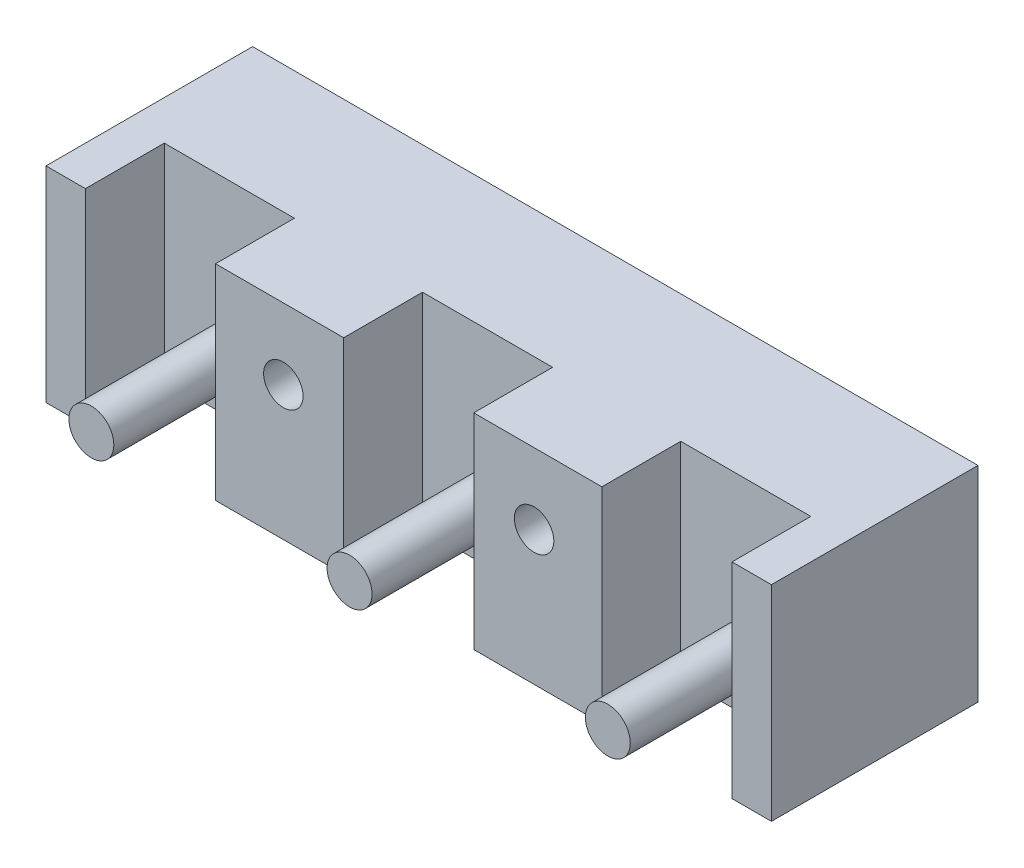
SolidWorks part; units mm, degrees
ref_plane "Plano frontal" through (0, 0, 0) normal (0, 0, 1) x (1, 0, 0)
ref_plane "Plano superior" through (0, 0, 0) normal (0, 1, 0) x (1, 0, 0)
ref_plane "Plano direito" through (0, 0, 0) normal (1, 0, 0) x (0, 0, -1)
sketch "Esboço1" plane through (0, 0, 0) normal (0, 0, 1) x (1, 0, 0)
  line L1 (46, 13) -> (-46, 13)
  line L2 (46, 13) -> (46, -13)
  line L3 (46, -13) -> (-46, -13)
  line L4 (-46, 13) -> (-46, -13)
  line L5 (46, 13) -> (-46, -13) construction
  line L6 (46, -13) -> (-46, 13) construction
  point P0 (0, 0)
  dimension "D1" = 26
  dimension "D2" = 92
extrude "Ressalto-extrusão1" add sketch "Esboço1" along normal blind 26.2
sketch "Esboço2" plane through (0, -13, 0) normal (0, -1, 0) x (1, 0, 0)
  line L0 (-41, 26.2) -> (-41, 16.2)
  line L1 (-46, 26.2) -> (46, 26.2) construction
  line L2 (-41, 16.2) -> (-24.5, 16.2)
  line L3 (-24.5, 16.2) -> (-24.5, 26.2)
  line L4 (-24.5, 26.2) -> (-41, 26.2)
  line L5 (-41, 16.2) -> (-46, 16.2) construction
  line L6 (-8.25, 26.2) -> (8.25, 26.2)
  line L7 (-8.25, 26.2) -> (-8.25, 16.2)
  line L8 (-8.25, 16.2) -> (8.25, 16.2)
  line L9 (8.25, 26.2) -> (8.25, 16.2)
  line L14 (41, 16.2) -> (24.5, 16.2)
  line L15 (41, 16.2) -> (41, 26.2)
  line L16 (41, 26.2) -> (24.5, 26.2)
  line L17 (24.5, 16.2) -> (24.5, 26.2)
  line L18 (-46, 26.2) -> (-46, 0) construction
  line L19 (41, 16.2) -> (46, 16.2) construction
  line L20 (46, 26.2) -> (46, 0) construction
  line L21 (0, 0) -> (0, 26.2) construction
  point P23 (0, 16.2)
  dimension "D1" = 16.5
  dimension "D2" = 5
  dimension "D3" = 10
extrude "Corte-extrusão1" cut sketch "Esboço2" against normal through all
sketch "Esboço3" plane through (0, 0, 0) normal (0, 0, -1) x (-1, 0, 0)
  line L0 (-15.9, 4) -> (15.9, 4) construction
  line L1 (0, -13) -> (0, 13) construction
  line L2 (46, -13) -> (-46, -13) construction
  line L3 (-46, 13) -> (46, 13) construction
  circle A0 centre (-15.9, 4) radius 2.5
  circle A1 centre (15.9, 4) radius 2.5
  point P12 (0, 4)
  dimension "D2" = 5
  dimension "D1" = 31.8
  dimension "D3" = 9
extrude "Corte-extrusão2" cut sketch "Esboço3" against normal through all
sketch "Esboço4" plane through (0, 0, 16.2) normal (0, 0, 1) x (1, 0, 0)
  line L0 (46, -5.85) -> (-46, -5.85) construction
  line L1 (46, -13) -> (46, 13) construction
  line L2 (-46, 13) -> (-46, -13) construction
  line L3 (24.5, -5.85) -> (41, -5.85) construction
  line L6 (-41, -5.85) -> (-24.5, -5.85) construction
  line L7 (-41, 13) -> (-41, -13) construction
  line L8 (-24.5, 13) -> (-24.5, -13) construction
  line L9 (24.5, 13) -> (24.5, -13) construction
  line L10 (41, 13) -> (41, -13) construction
  line L11 (8.25, -13) -> (24.5, -13) construction
  circle A0 centre (0, -5.85) radius 2.85
  circle A1 centre (32.75, -5.85) radius 2.85
  circle A2 centre (-32.75, -5.85) radius 2.85
  point P24 (32.75, -5.85)
  point P25 (-32.75, -5.85)
  dimension "D1" = 5.7
  dimension "D2" = 7.15
extrude "Ressalto-extrusão2" add sketch "Esboço4" along normal blind 17.5
